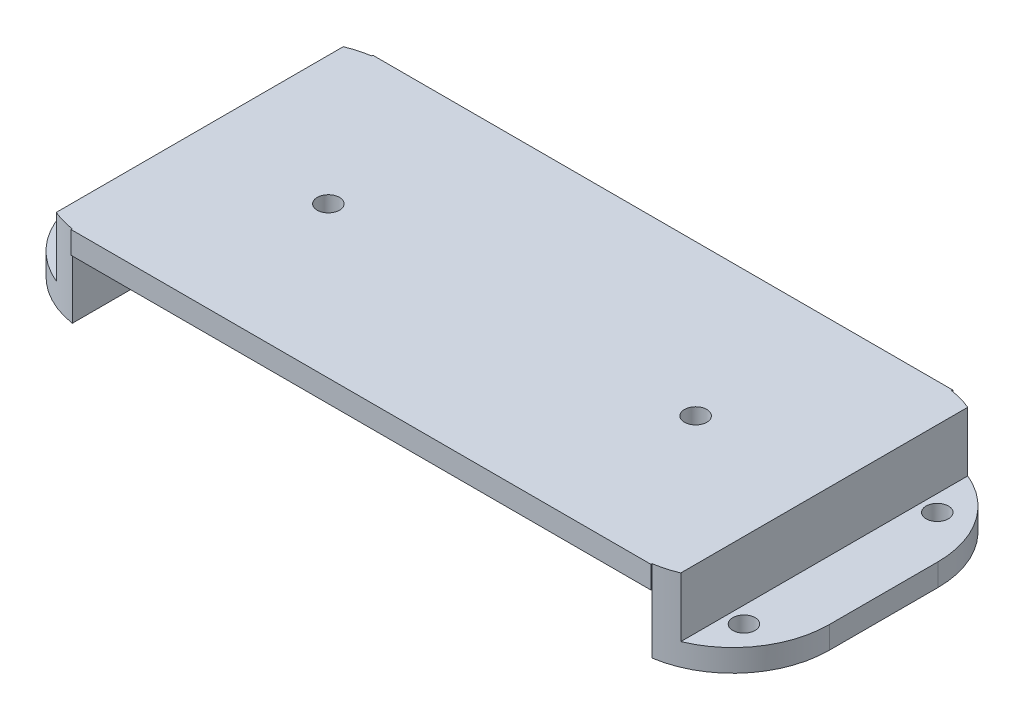
SolidWorks part; units mm, degrees
ref_plane "Front Plane" through (0, 0, 0) normal (0, 0, 1) x (1, 0, 0)
ref_plane "Top Plane" through (0, 0, 0) normal (0, 1, 0) x (1, 0, 0)
ref_plane "Right Plane" through (0, 0, 0) normal (1, 0, 0) x (0, 0, -1)
sketch "Sketch1" plane through (0, 0, 0) normal (0, 0, 1) x (1, 0, 0)
  line L17 (8.1252, -6.6) -> (92.1252, -6.6)
  line L18 (8.1252, -6.6) -> (8.1252, -3.6)
  line L19 (8.1252, -3.6) -> (92.1252, -3.6)
  line L20 (92.1252, -6.6) -> (92.1252, -3.6)
  line L25 (92.1252, -6.6) -> (89.1252, -6.6)
  line L26 (92.1252, -6.6) -> (92.1252, -14.6)
  line L27 (92.1252, -14.6) -> (89.1252, -14.6)
  line L28 (89.1252, -6.6) -> (89.1252, -14.6)
  line L29 (92.1252, -14.6) -> (100.1252, -14.6)
  line L30 (92.1252, -14.6) -> (92.1252, -11.6)
  line L31 (92.1252, -11.6) -> (100.1252, -11.6)
  line L32 (100.1252, -14.6) -> (100.1252, -11.6)
  line L33 (50.1252, -6.6) -> (35.1252, -6.6)
  line L40 (31.87, -14.6) -> (31.87, -11.6)
  line L41 (8.1252, -6.6) -> (11.1252, -6.6)
  line L42 (8.1252, -6.6) -> (8.1252, -14.6)
  line L43 (8.1252, -14.6) -> (11.1252, -14.6)
  line L44 (11.1252, -6.6) -> (11.1252, -14.6)
  line L45 (8.1252, -11.6) -> (0.1252, -11.6)
  line L46 (8.1252, -11.6) -> (8.1252, -14.6)
  line L47 (8.1252, -14.6) -> (0.1252, -14.6)
  line L48 (0.1252, -11.6) -> (0.1252, -14.6)
  point P11 (0, 0)
  dimension "D2" = 3
  dimension "D3" = 3
  dimension "D4" = 3
  dimension "D5" = 8
  dimension "D6" = 8
  dimension "D7" = 8
  dimension "D8" = 8
  dimension "D9" = 3
  dimension "D10" = 3
  dimension "D11" = 100
extrude "Boss-Extrude1" add sketch "Sketch1" along normal blind 40.6
sketch "Sketch2" plane through (0, -14.6, 0) normal (0, -1, 0) x (1, 0, 0)
  line L3 (0.1252, 0) -> (11.1252, 0) construction
  line L4 (89.1252, 0) -> (100.1252, 0)
  line L5 (100.1252, 0) -> (100.1252, 40.6)
  line L6 (100.1252, 40.6) -> (89.1252, 40.6)
  line L7 (89.1252, 40.6) -> (89.1252, 0)
  line L8 (89.1252, 0) -> (87.1252, 0)
  line L9 (100.1252, 13) -> (100.1252, 27.6)
  line L10 (87.1252, 40.6) -> (89.1252, 40.6)
  line L11 (89.1252, 40.6) -> (89.1252, 0)
  line L12 (11.1252, 0) -> (11.1252, 40.6) construction
  line L13 (11.1252, 40.6) -> (0.1252, 40.6) construction
  line L14 (0.1252, 40.6) -> (0.1252, 0) construction
  line L15 (11.1252, 0) -> (89.1252, 0) construction
  line L16 (89.1252, 0) -> (89.1252, 40.6) construction
  line L17 (89.1252, 40.6) -> (11.1252, 40.6) construction
  line L18 (11.1252, 40.6) -> (11.1252, 0) construction
  line L19 (0.1252, 0) -> (11.1252, 0)
  line L20 (11.1252, 0) -> (11.1252, 40.6)
  line L21 (11.1252, 40.6) -> (0.1252, 40.6)
  line L22 (0.1252, 40.6) -> (0.1252, 0)
  line L23 (11.1252, 0) -> (89.1252, 0)
  line L24 (89.1252, 0) -> (89.1252, 40.6)
  line L25 (89.1252, 40.6) -> (11.1252, 40.6)
  line L26 (11.1252, 40.6) -> (11.1252, 0)
  line L27 (50.1252, 40.6) -> (50.1252, 0) construction
  line L28 (0.1252, 13) -> (0.1252, 27.6)
  circle A2 centre (94.3252, 33.3) radius 1.5
  circle A3 centre (94.3252, 7.3) radius 1.5
  arc A4 (87.1252, 0) -> (100.1252, 13) centre (87.1252, 13) ccw
  arc A5 (100.1252, 27.6) -> (87.1252, 40.6) centre (87.1252, 27.6) ccw
  circle A6 centre (5.9252, 33.3) radius 1.5
  circle A7 centre (5.9252, 7.3) radius 1.5
  arc A8 (13.1252, 0) -> (0.1252, 13) centre (13.1252, 13) cw
  arc A9 (0.1252, 27.6) -> (13.1252, 40.6) centre (13.1252, 27.6) cw
  line M5 (89.1252, 0) -> (100.1252, 0)
  line M6 (100.1252, 0) -> (100.1252, 40.6)
  line M7 (100.1252, 40.6) -> (89.1252, 40.6)
  dimension "D2" = 3
  dimension "D3" = 3
  dimension "D4" = 5.2
  dimension "D6" = 7.3
  dimension "D7" = 7.3
  dimension "D8" = 13
  dimension "D5" = 5.2
  dimension "D1" = 0
extrude "Cut-Extrude3" cut sketch "Sketch2" against normal blind 24 contours A2 | A5 M6 M7 | A4 M5 M6 | A3 | L22 A9 L20 L21 | L20 A8 L22 L19 | A6 | A7
sketch "Sketch5" plane through (0, -3.6, 0) normal (0, 1, 0) x (1, 0, 0)
  line L0 (11.1252, 0) -> (89.1252, 0) construction
  line L1 (8.1252, -39.6) -> (8.1252, -1) construction
  line L2 (50.1252, 0) -> (50.1252, -40.6) construction
  line L6 (89.1252, 0) -> (11.1252, 0)
  line L7 (8.1252, -1) -> (8.1252, -39.6)
  line L8 (11.1252, -40.6) -> (89.1252, -40.6)
  line L9 (92.1252, -39.6) -> (92.1252, -1)
  line L10 (89.1252, 0) -> (11.1252, 0)
  line L11 (8.1252, -1) -> (8.1252, -39.6)
  line L12 (11.1252, -40.6) -> (89.1252, -40.6)
  line L13 (92.1252, -39.6) -> (92.1252, -1)
  line L17 (89.1252, -40.6) -> (89.1252, -40.4452)
  line L18 (89.1252, -40.6) -> (89.1252, -40.4452)
  line L19 (89.1252, -0.1548) -> (89.1252, 0)
  line L20 (89.1252, -0.1548) -> (89.1252, 0)
  line L23 (11.1252, -40.4452) -> (11.1252, -40.6)
  line L24 (11.1252, -40.4452) -> (11.1252, -40.6)
  line L25 (11.1252, 0) -> (11.1252, -0.1548)
  line L26 (11.1252, 0) -> (11.1252, -0.1548)
  circle A0 centre (25.4252, -20.3) radius 1.5
  circle A1 centre (74.8252, -20.3) radius 1.5
  arc A4 (89.1252, -40.4452) -> (92.1252, -39.6) centre (87.1252, -27.6) ccw
  arc A5 (89.1252, -40.4452) -> (92.1252, -39.6) centre (87.1252, -27.6) ccw
  arc A6 (92.1252, -1) -> (89.1252, -0.1548) centre (87.1252, -13) ccw
  arc A7 (92.1252, -1) -> (89.1252, -0.1548) centre (87.1252, -13) ccw
  arc A10 (11.1252, -0.1548) -> (8.1252, -1) centre (13.1252, -13) ccw
  arc A11 (11.1252, -0.1548) -> (8.1252, -1) centre (13.1252, -13) ccw
  arc A12 (8.1252, -39.6) -> (11.1252, -40.4452) centre (13.1252, -27.6) ccw
  arc A13 (8.1252, -39.6) -> (11.1252, -40.4452) centre (13.1252, -27.6) ccw
  dimension "D1" = 3
  dimension "D2" = 20.3
  dimension "D3" = 17.3
  dimension "D4" = 0
extrude "Cut-Extrude4" cut sketch "Sketch5" against normal blind 4 contours A0 | A1
sketch "Sketch7" plane through (0, -3.6, 0) normal (0, 1, 0) x (1, 0, 0)
  line L4 (89.1252, 0) -> (11.1252, 0)
  line L5 (8.1252, -1) -> (8.1252, -39.6)
  line L6 (11.1252, -40.6) -> (89.1252, -40.6)
  line L7 (92.1252, -39.6) -> (92.1252, -1)
  line L8 (89.1252, 0) -> (11.1252, 0)
  line L9 (8.1252, -1) -> (8.1252, -39.6)
  line L10 (11.1252, -40.6) -> (89.1252, -40.6)
  line L11 (92.1252, -39.6) -> (92.1252, -1)
  line L14 (89.1252, -40.6) -> (89.1252, -40.4452)
  line L15 (89.1252, -40.6) -> (89.1252, -40.4452)
  line L16 (89.1252, -0.1548) -> (89.1252, 0)
  line L17 (89.1252, -0.1548) -> (89.1252, 0)
  line L20 (11.1252, -40.4452) -> (11.1252, -40.6)
  line L21 (11.1252, -40.4452) -> (11.1252, -40.6)
  line L22 (11.1252, 0) -> (11.1252, -0.1548)
  line L23 (11.1252, 0) -> (11.1252, -0.1548)
  arc A2 (89.1252, -40.4452) -> (92.1252, -39.6) centre (87.1252, -27.6) ccw
  arc A3 (89.1252, -40.4452) -> (92.1252, -39.6) centre (87.1252, -27.6) ccw
  arc A4 (92.1252, -1) -> (89.1252, -0.1548) centre (87.1252, -13) ccw
  arc A5 (92.1252, -1) -> (89.1252, -0.1548) centre (87.1252, -13) ccw
  arc A8 (11.1252, -0.1548) -> (8.1252, -1) centre (13.1252, -13) ccw
  arc A9 (11.1252, -0.1548) -> (8.1252, -1) centre (13.1252, -13) ccw
  arc A10 (8.1252, -39.6) -> (11.1252, -40.4452) centre (13.1252, -27.6) ccw
  arc A11 (8.1252, -39.6) -> (11.1252, -40.4452) centre (13.1252, -27.6) ccw
  dimension "D1" = 0
